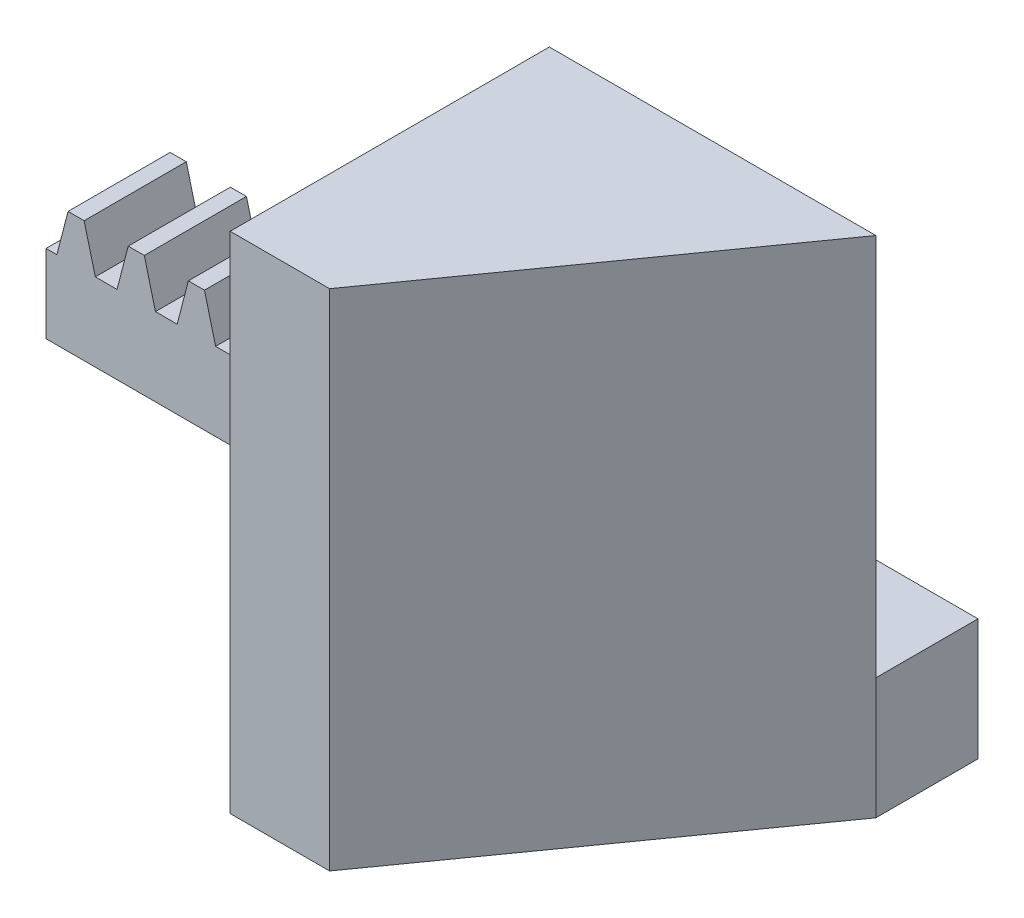
SolidWorks part; units mm, degrees
extrude "Blank" add sketch "BlankSke" against normal blind 8
sketch "BlankSke" plane through (0, 0, 0) normal (0, 0, 1) x (1, 0, 0)
  line L1 (0, 0) -> (50, 0)
  line L2 (0, 0) -> (0, 9.5)
  line L3 (0, 9.5) -> (50, 9.5)
  line L4 (50, 0) -> (50, 9.5)
  dimension "Length" = 50
  dimension "Blank_height" = 9.5
ref_plane "Plane1" through (0, 0, 0) normal (0, 0, 1) x (1, 0, 0)
ref_plane "Plane2" through (0, 0, 0) normal (0, 1, 0) x (1, 0, 0)
ref_plane "Plane3" through (0, 0, 0) normal (1, 0, 0) x (0, 0, -1)
other "Configuration Table"
sketch "HoldingSke" plane through (0, 0, 0) normal (0, 1, 0) x (1, 0, 0)
  line L0 (0, 0) -> (0.0928, 0.6602)
  line L1 (-15, 0) -> (100, 0) construction
  line L2 (0, 0) -> (-2.1039, 2.3779)
  line L3 (0, 0) -> (-11.863, 4.5341)
  line L4 (0, 0) -> (8.4473, 1.7955)
  line L5 (0, 0) -> (-23.7986, -8.8762)
  line L6 (0, 0) -> (-10.5278, -7.1032)
  line L9 (-67.7845, 28.3722) -> (-19.3772, 40.8912)
  line L10 (-76.2, 3.8779) -> (-68.2, 3.8779)
  line L11 (0, 0) -> (-8, 0)
  line L12 (-76.2, 101.6) -> (-76.147, 101.6)
  line L13 (24.9733, 27.94) -> (52.9518, 28.4284)
  line L14 (24.9733, 27.94) -> (24.9743, 27.94)
  line L15 (24.9733, 27.94) -> (100.4006, 29.5858)
  circle A0 centre (0, 0) radius 19.05
  circle A1 centre (0, 0) radius 4
  circle A2 centre (0, 0) radius 12.7
  dimension "MPH" = 8
  dimension "Diameter" = 38.1
  dimension "Num_teeth" = 12
  dimension "Pitch" = 0.6667
  dimension "Show_teeth" = 998
  dimension "Thickness" = 12.7
  dimension "Ap" = 14.5
  dimension "Pitch_height" = 8
  dimension "Width" = 8
  dimension "Backlash" = 0.053
  dimension "Addendum_fac" = 1
  dimension "Dedendum_fac" = 1.25
  dimension "Clearance_fac" = 0.25
  dimension "Dedendum_add" = 0.001
  dimension "Length" = 50
  dimension "Module" = 1.5
sketch "TooCutSkeIll" plane through (0, 0, 0) normal (0, 0, 1) x (1, 0, 0)
  line L0 (-1.7134, 9.455) -> (-0.9251, 6.4069)
  line L1 (-0.5611, 6.125) -> (0.5611, 6.125)
  line L2 (0.9251, 6.4069) -> (1.7134, 9.455)
  line L3 (50, 9.5) -> (0, 9.5) construction
  line L4 (0, 0) -> (0, 64.897) construction
  line L5 (-13.208, 8) -> (12.954, 8) construction
  line L6 (0, 0) -> (50, 0) construction
  line L7 (1.3371, 8) -> (1.3371, 48.7463) construction
  line L8 (-1.3371, 8) -> (-1.3371, 48.7463) construction
  line L9 (1.7715, 9.5) -> (1.7715, 9.5254)
  line L10 (-1.7715, 9.5) -> (-1.7715, 9.5254)
  line L11 (-1.7715, 9.5254) -> (1.7715, 9.5254)
  arc A0 (0.5611, 6.125) -> (0.9251, 6.4069) centre (0.5611, 6.501) ccw
  arc A1 (-0.9251, 6.4069) -> (-0.5611, 6.125) centre (-0.5611, 6.501) ccw
  arc A2 (1.7715, 9.5) -> (1.7134, 9.455) centre (1.7715, 9.44) ccw
  arc A3 (-1.7134, 9.455) -> (-1.7715, 9.5) centre (-1.7715, 9.44) ccw
  dimension "Pitch_height" = 8
  dimension "Addendum_plus" = 1.5254
  dimension "Pressure_angle" = 14.5
  dimension "Gap_width" = 2.6742
  dimension "Dedendum" = 1.875
extrude "ToothCutIll" [suppressed] cut sketch "TooCutSkeIll" against normal through all
sketch "TooCutSkeSim" plane through (0, 0, 0) normal (0, 0, 1) x (1, 0, 0)
  line L0 (0.8522, 6.125) -> (-0.8522, 6.125)
  line L1 (1.7316, 9.5254) -> (0.8522, 6.125)
  line L2 (0, 17.4625) -> (0, 53.467) construction
  line L3 (1.7316, 9.5254) -> (-1.7316, 9.5254)
  line L6 (-1.7316, 9.5254) -> (-0.8522, 6.125)
  line L9 (-1.3371, 8) -> (1.3371, 8) construction
  line L10 (0, 0) -> (50, 0) construction
  line L11 (1.3371, 8) -> (1.3371, 53.467) construction
  line L12 (-1.3371, 8) -> (-1.3371, 53.467) construction
  dimension "Pitch_height" = 8
  dimension "Addendum_plus" = 1.5254
  dimension "Pressure_angle" = 14.5
  dimension "Gap_width" = 2.6742
  dimension "Dedendum" = 1.875
extrude "ToothCutSim" cut sketch "TooCutSkeSim" against normal through all
pattern_linear "TeethCuts" count 11 spacing 4.7124 along (1, 0, 0) of "ToothCutIll", "ToothCutSim"
sketch "Sketch3" plane through (50, 0, 0) normal (1, 0, 0) x (0, 0, -1)
  line L1 (0, 9.5) -> (8, 9.5)
  line L2 (0, 9.5) -> (0, 0)
  line L3 (0, 0) -> (8, 0)
  line L4 (8, 9.5) -> (8, 0)
extrude "Boss-Extrude2" add sketch "Sketch3" along normal blind 15
sketch "Sketch5" [suppressed] plane through (0, 9.5, 0) normal (0, 1, 0) x (1, 0, 0)
  line L1 (39.4241, 8) -> (55, 8)
  line L2 (39.4241, 8) -> (39.4241, 0)
  line L3 (39.4241, 0) -> (55, 0)
  line L4 (55, 8) -> (55, 0)
extrude "Boss-Extrude3" [suppressed] add sketch "Sketch5" along normal blind 30
sketch "Sketch7" plane through (0, 0, 0) normal (0, 1, 0) x (1, 0, 0)
  line L4 (65, 0) -> (39.4241, 0)
  line L5 (0, 0) -> (65, 0) construction
  line L9 (39.4241, 0) -> (39.4241, -25)
  line L10 (39.4241, -25) -> (47.2121, -25)
  line L11 (47.2121, -25) -> (65, 0)
extrude "Boss-Extrude5" add sketch "Sketch7" along normal blind 39.5
sketch "Sketch8" [suppressed] plane through (0, 0, -8) normal (0, 0, -1) x (-1, 0, 0)
  line L1 (-39.4241, 9.5) -> (-55, 9.5)
  line L2 (-39.4241, 9.5) -> (-39.4241, 39.5)
  line L3 (-39.4241, 39.5) -> (-55, 39.5)
  line L4 (-55, 9.5) -> (-55, 39.5)
extrude "Cut-Extrude1" [suppressed] cut sketch "Sketch8" against normal blind 11
equation "' \"Module@HoldingSke\" = 6.35"
equation "' \"Num_teeth@HoldingSke\" = 12"
equation "' \"Ap@HoldingSke\" =  20"
equation "' \"Ap@HoldingSke\" = 20"
equation "' \"Width@HoldingSke\" = 0.25 * 25.4"
equation "' \"Show_teeth@HoldingSke\" = 500"
equation "' \"Backlash@HoldingSke\" = 0.009 * 25.4"
equation "' \"Addendum_fac@HoldingSke\" = 1.0"
equation "' \"Dedendum_fac@HoldingSke\" = 1.25"
equation "' \"Dedendum_add@HoldingSke\" = 0.00005 * 25.4"
equation "' \"Clearance_fac@HoldingSke\" = 0.25"
equation "' \"Pitch_height@HoldingSke\" = 1 * 25.4"
equation "' \"Length@HoldingSke\" = 4.71 * 25.4"
equation "\"Pitch@HoldingSke\" = 1 / \"Module@HoldingSke\""
equation "\"MPH@HoldingSke\" = \"Dedendum_fac@HoldingSke\" / \"Pitch@HoldingSke\" + 2 * \"Dedendum_add@HoldingSke\" + 0.002 * 25.4"
equation "\"MPH@HoldingSke\" = ((sgn( \"MPH@HoldingSke\" - \"Pitch_height@HoldingSke\")+1)*( \"MPH@HoldingSke\" - \"Pitch_height@HoldingSke\"))/2 + \"Pitch_height@HoldingSke\""
equation "\"Blank_height@BlankSke\" = \"Pitch_height@HoldingSke\" + \"Addendum_fac@HoldingSke\"  / \"Pitch@HoldingSke\" "
equation "\"Length@BlankSke\" =  \"Length@HoldingSke\""
equation "\"Face_width@Blank\" = \"Width@HoldingSke\""
equation "\"Pressure_angle@TooCutSkeIll\" = \"Ap@HoldingSke\""
equation "\"Addendum_plus@TooCutSkeIll\" =  \"Addendum_fac@HoldingSke\"  / \"Pitch@HoldingSke\" + 0.001 *25.4"
equation "\"Dedendum@TooCutSkeIll\" = \"Dedendum_fac@HoldingSke\"  / \"Pitch@HoldingSke\""
equation "\"Pitch_height@TooCutSkeIll\" =  \"MPH@HoldingSke\""
equation "\"Gap_width@TooCutSkeIll\" = 3.14159265 / 2 / \"Pitch@HoldingSke\" + 6 * \"Backlash@HoldingSke\""
equation "\"Pressure_angle@TooCutSkeSim\" = \"Ap@HoldingSke\""
equation "\"Addendum_plus@TooCutSkeSim\" =  \"Addendum_fac@HoldingSke\"  / \"Pitch@HoldingSke\" + 0.001 * 25.4"
equation "\"Dedendum@TooCutSkeSim\" = \"Dedendum_fac@HoldingSke\"  / \"Pitch@HoldingSke\""
equation "\"Pitch_height@TooCutSkeSim\" =  \"MPH@HoldingSke\""
equation "\"Gap_width@TooCutSkeSim\" = 3.14159265 / 2 / \"Pitch@HoldingSke\" + 6 * \"Backlash@HoldingSke\""
equation "\"Root_fillet@TooCutSkeIll\" = \"Clearance_fac@HoldingSke\" / \"Pitch@HoldingSke\" + \"Dedendum_add@HoldingSke\""
equation "\"Break_rad@TooCutSkeIll\" = 0.02 / \"Pitch@HoldingSke\" * 2"
equation "\"Linear_pitch@TeethCuts\" = 3.14159265 / \"Pitch@HoldingSke\""
equation "\"Num_teeth@HoldingSke\" = int( ( \"Length@HoldingSke\" + 0 ) / (3.14159265 / \"Pitch@HoldingSke\")) + 0.9999  + 1"
equation " \"Num_teeth@TeethCuts\" = int( \"Show_teeth@HoldingSke\" ) + 1"
equation " \"Num_teeth@TeethCuts\" = ((sgn( \"Num_teeth@TeethCuts\" - \"Num_teeth@HoldingSke\" )-1)*( \"Num_teeth@TeethCuts\" - \"Num_teeth@HoldingSke\" ))/-2+ \"Num_teeth@HoldingSke\""
equation " \"Num_teeth@TeethCuts\" = ((sgn( \"Num_teeth@TeethCuts\" - 2.0)+1)*( \"Num_teeth@TeethCuts\" - 2.0))/2 +2.0"
